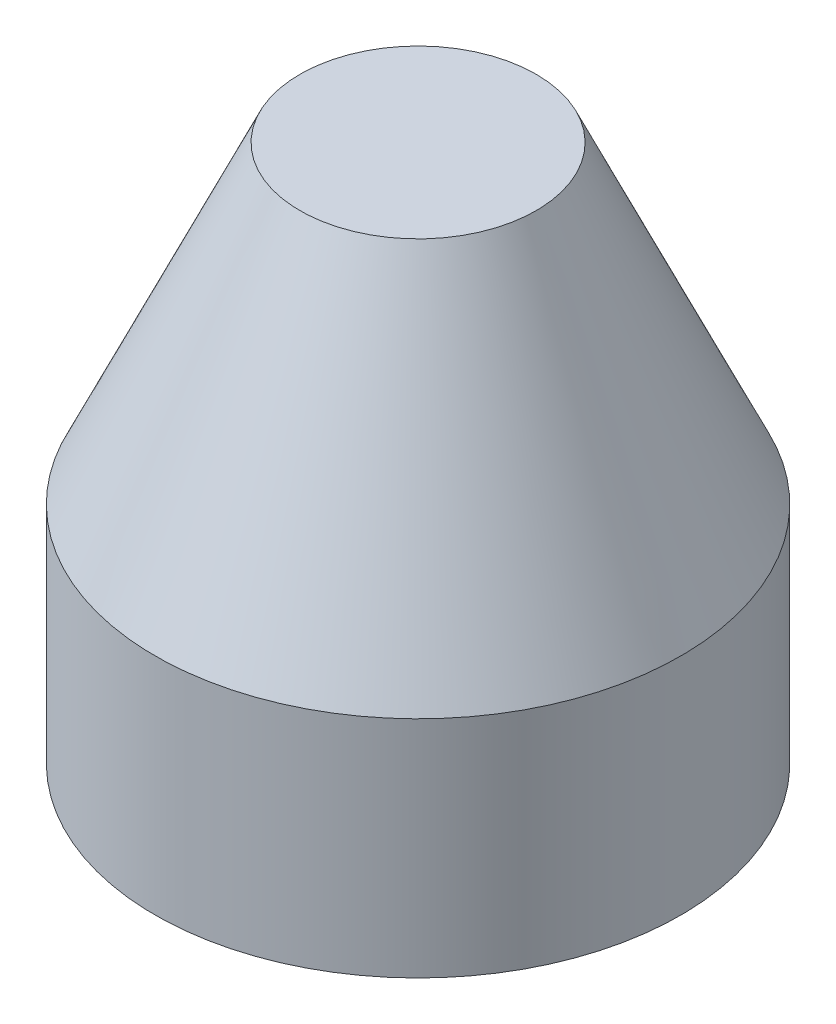
SolidWorks part; units mm, degrees
ref_plane "Front Plane" through (0, 0, 0) normal (0, 0, 1) x (1, 0, 0)
ref_plane "Top Plane" through (0, 0, 0) normal (0, 1, 0) x (1, 0, 0)
ref_plane "Right Plane" through (0, 0, 0) normal (1, 0, 0) x (0, 0, -1)
sketch "Sketch1" plane through (0, 0, 0) normal (0, 0, 1) x (1, 0, 0)
  line L0 (0, 0) -> (0, 45.5188)
  line L1 (0, 0) -> (22.25, 0)
  line L2 (22.25, 0) -> (22.25, 19)
  line L3 (22.25, 19) -> (10, 45.5188)
  line L4 (10, 45.5188) -> (0, 45.5188)
  line L5 (0, 32.53) -> (16, 32.53) construction
  point P8 (0, 0)
  dimension "D1" = 19
  dimension "D2" = 22.25
  dimension "D3" = 16
  dimension "D4" = 13.53
  dimension "D5" = 10
revolve "Revolve1" add sketch "Sketch1" angle 360 about L0
hole_wizard "Ø12.0mm Dowel Hole1" positions "Sketch2" profile "Sketch3" hole size "Ø12.0" standard "ANSI Metric"
sketch "Sketch2" plane through (0, 0, 0) normal (0, -1, 0) x (-1, 0, 0)
  point P0 (0, 0)
sketch "Sketch3" plane through (0, 0, 0) normal (1, 0, 0) x (0, 0, -1)
  line L0 (0, 0) -> (0, 23.6052)
  line L1 (0, 23.6052) -> (6, 20)
  line L2 (6, 20) -> (6, 0)
  line L5 (6, 0) -> (0, 0)
  line L10 (0, 23.6052) -> (-6, 20) construction
  line L11 (0, -6.35) -> (0, 107.95) construction
  dimension "Hole Dia." = 12
  dimension "Hole Depth" = 20
  dimension "Drill Angle" = 118
